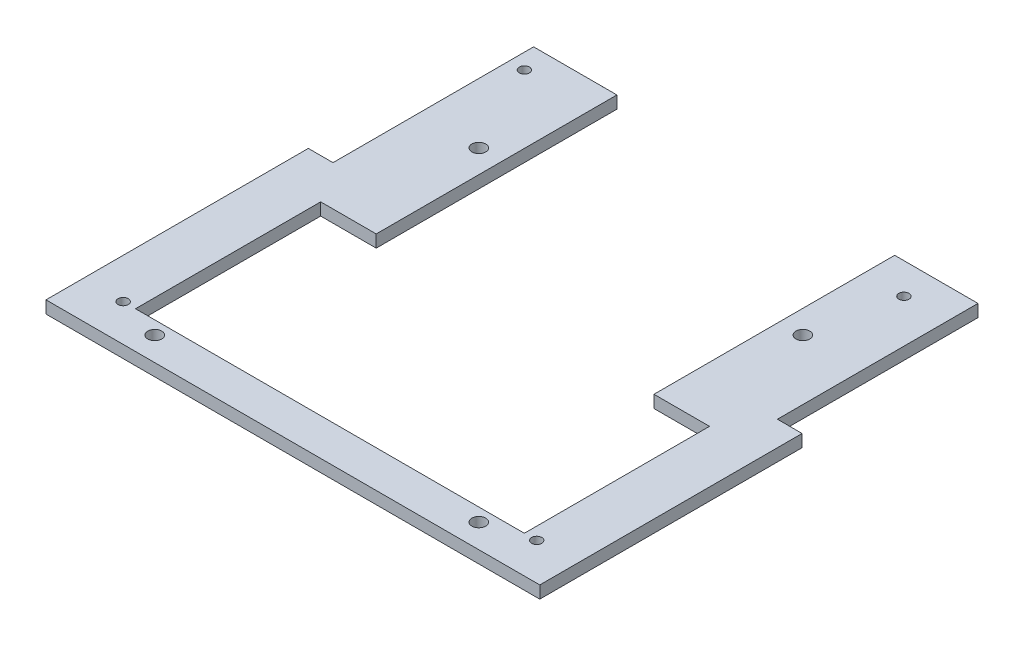
SolidWorks part; units mm, degrees
material "Acryl (halb- bis hochschlagzäh)"
ref_plane "Ebene vorne" through (0, 0, 0) normal (0, 0, 1) x (1, 0, 0)
ref_plane "Ebene oben" through (0, 0, 0) normal (0, 1, 0) x (1, 0, 0)
ref_plane "Ebene rechts" through (0, 0, 0) normal (1, 0, 0) x (0, 0, -1)
sketch "Sketch1" plane through (0, 0, 0) normal (0, 1, 0) x (1, 0, 0)
  line L1 (-80, -75) -> (80, -75)
  line L2 (-80, -75) -> (-80, 75)
  line L3 (-80, 75) -> (80, 75)
  line L4 (80, -75) -> (80, 75)
  line L5 (-80, -75) -> (80, 75) construction
  line L6 (-80, 75) -> (80, -75) construction
  line L7 (-63, -63) -> (63, -63)
  line L8 (-63, -63) -> (-63, -3)
  line L9 (-63, -3) -> (63, -3)
  line L10 (63, -63) -> (63, -3)
  line L11 (-45, -3) -> (45, -3)
  line L12 (-45, -3) -> (-45, 75)
  line L13 (-45, 75) -> (45, 75)
  line L14 (45, -3) -> (45, 75)
  line L15 (-80, 75) -> (-72, 75)
  line L16 (-80, 75) -> (-80, 10)
  line L17 (-80, 10) -> (-72, 10)
  line L18 (-72, 75) -> (-72, 10)
  line L19 (80, 75) -> (72, 75)
  line L20 (80, 75) -> (80, 10)
  line L21 (80, 10) -> (72, 10)
  line L22 (72, 75) -> (72, 10)
  circle A0 centre (-67, -63) radius 1.65
  circle A1 centre (67, -63) radius 1.65
  circle A2 centre (58, 65) radius 1.65
  circle A3 centre (-67, 67) radius 1.65
  point P0 (0, 0)
  dimension "D3" = 12
  dimension "D5" = 3.3
  dimension "D1" = 150
  dimension "D2" = 160
  dimension "D4" = 13
  dimension "D6" = 13
  dimension "D7" = 12
  dimension "D8" = 22
  dimension "D9" = 10
  dimension "D10" = 13
  dimension "D11" = 8
  dimension "D12" = 17
  dimension "D13" = 12
  dimension "D14" = 17
  dimension "D15" = 60
  dimension "D16" = 35
  dimension "D17" = 35
  dimension "D18" = 8
  dimension "D19" = 8
  dimension "D20" = 65
  dimension "D21" = 65
extrude "Extrude1" add sketch "Sketch1" along normal blind 4 contours L1 L4 L3 L2 A3 A2 A1 A0 L10 L7 L8 L9
sketch "Sketch3" plane through (0, 4, 0) normal (0, 1, 0) x (1, 0, 0)
  line L1 (-60, -74.7598) -> (60, -74.7598) construction
  line L2 (-60, -74.7598) -> (-60, 45.2402) construction
  line L3 (-60, 45.2402) -> (60, 45.2402) construction
  line L4 (60, -74.7598) -> (60, 45.2402) construction
  circle A0 centre (52.5, -67.2598) radius 2.25
  circle A1 centre (-52.5, -67.2598) radius 2.25
  circle A2 centre (52.5, 37.7402) radius 2.25
  circle A3 centre (-52.5, 37.7402) radius 2.25
  dimension "D2" = 7.5
  dimension "D4" = 7.5
  dimension "D6" = 7.5
  dimension "D8" = 7.5
  dimension "D10" = 4.5
  dimension "D1" = 120
  dimension "D3" = 7.5
  dimension "D5" = 7.5
  dimension "D7" = 7.5
  dimension "D9" = 7.5
  dimension "D11" = 20
extrude "Extrude3" cut sketch "Sketch3" against normal blind 4
